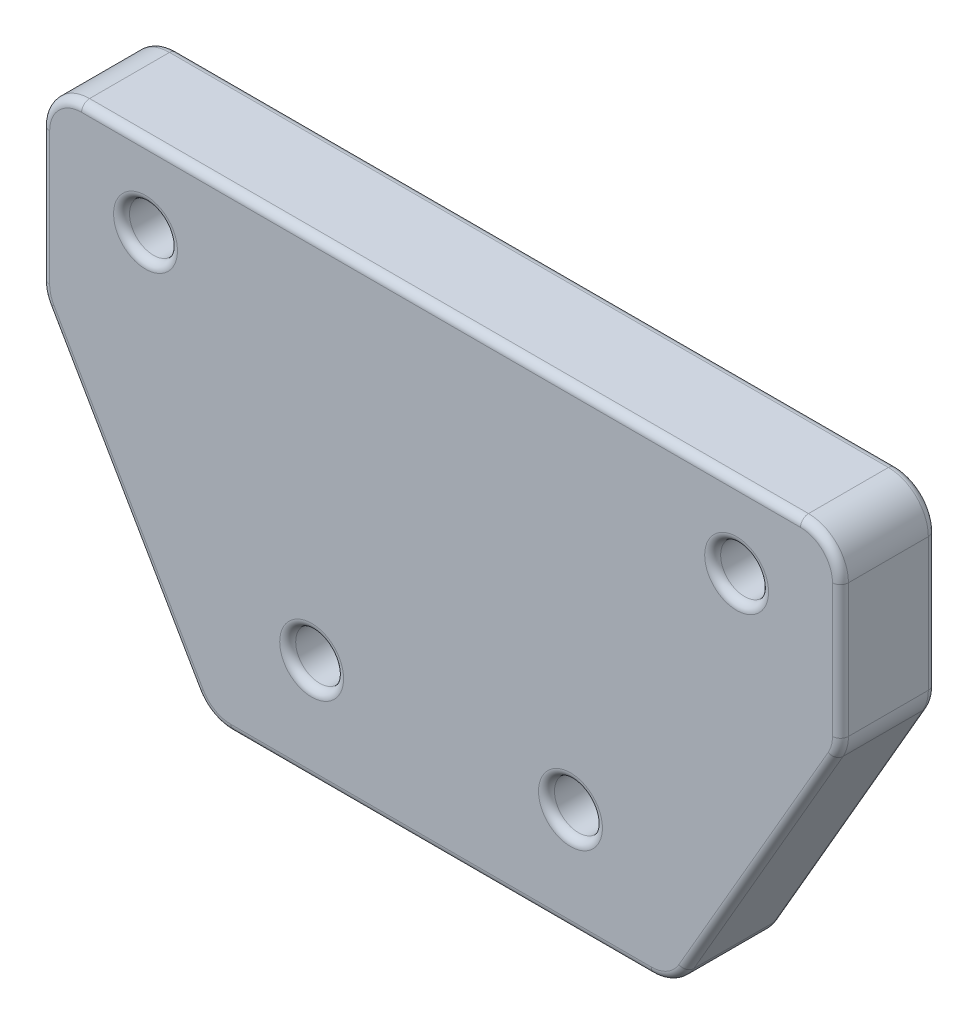
SolidWorks part; units mm, degrees
ref_plane "Front Plane" through (0, 0, 0) normal (0, 0, 1) x (1, 0, 0)
ref_plane "Top Plane" through (0, 0, 0) normal (0, 1, 0) x (1, 0, 0)
ref_plane "Right Plane" through (0, 0, 0) normal (1, 0, 0) x (0, 0, -1)
sketch "Sketch1" plane through (0, 0, 0) normal (0, 0, 1) x (1, 0, 0)
  line L0 (-14.6, -44.3) -> (14.6, -44.3)
  line L1 (-14.6, -37.8) -> (-14.6, -65.5) construction
  line L2 (14.6, -65.5) -> (14.6, -37.8) construction
  line L3 (-8.1, -39.3) -> (-8.1, -44.3) construction
  line L4 (14.6, -44.3) -> (25, -26.3)
  line L6 (25, -26.3) -> (25, -14.8)
  line L7 (25, -19.8) -> (25, -0.8) construction
  line L8 (25, -14.8) -> (-25, -14.8)
  line L9 (-25, -0.8) -> (-25, -19.8) construction
  line L10 (-25, -14.8) -> (-25, -26.3)
  line L11 (24.5, -13.8) -> (12.5, -13.8) construction
  line L12 (-14.6, -44.3) -> (-25, -26.3)
  circle A0 centre (-18.5, -19.8) radius 1.5 construction
  circle A1 centre (18.5, -19.8) radius 1.5 construction
  circle A2 centre (8.1, -37.8) radius 1.5 construction
  circle A3 centre (-8.1, -37.8) radius 1.5 construction
  circle A4 centre (-18.5, -19.8) radius 1.5
  circle A5 centre (18.5, -19.8) radius 1.5
  circle A6 centre (8.1, -37.8) radius 1.5
  circle A7 centre (-8.1, -37.8) radius 1.5
  arc A8 (12, -19.8) -> (25, -19.8) centre (18.5, -19.8) ccw construction
  point P34 (18.5, -26.3)
  dimension "D1" = 5
  dimension "D2" = 1
extrude "Boss-Extrude1" add sketch "Sketch1" along normal blind 6
fillet "Fillet1" radius 2.5 6 edges at (25, -14.8, 3) (25, -26.3, 3) (14.6, -44.3, 3) (-25, -14.8, 3) (-25, -26.3, 3) (-14.6, -44.3, 3)
fillet "Fillet2" radius 0.5 32 edges at (-6.6, -37.8, 0) (20, -19.8, 0) (-24.2678, -15.5322, 0) (-25, -21.4648, 0) (-24.9147, -26.2771, 0) (-19.9932, -34.9655, 0) (-14.4068, -43.9653, 0) (0, -44.3, 0) (14.4068, -43.9653, 0) (19.9932, -34.9655, 0) (24.9147, -26.2771, 0) (25, -21.4648, 0) (24.2678, -15.5322, 0) (0, -14.8, 0) (-17, -19.8, 0) (9.6, -37.8, 0) (-6.6, -37.8, 6) (9.6, -37.8, 6) (20, -19.8, 6) (-17, -19.8, 6) (24.9147, -26.2771, 6) (19.9932, -34.9655, 6) (14.4068, -43.9653, 6) (0, -44.3, 6) (-14.4068, -43.9653, 6) (-19.9932, -34.9655, 6) (-24.9147, -26.2771, 6) (-25, -21.4648, 6) (-24.2678, -15.5322, 6) (0, -14.8, 6) (24.2678, -15.5322, 6) (25, -21.4648, 6)
